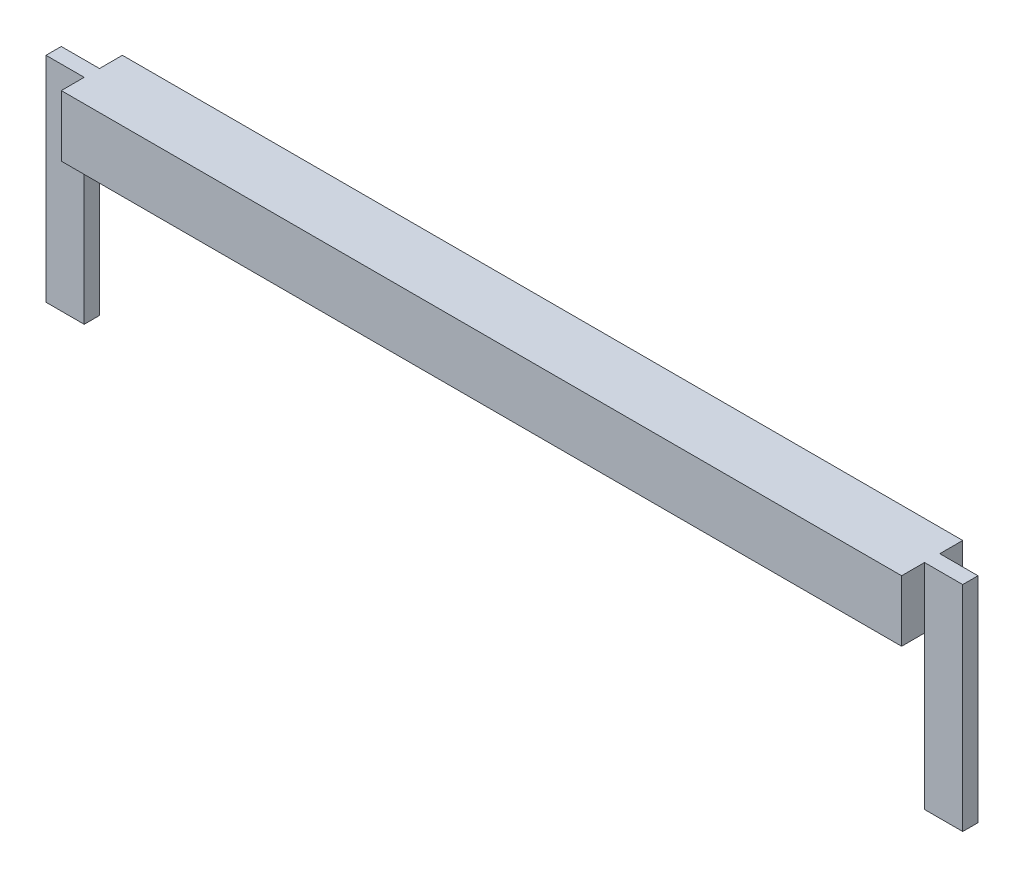
SolidWorks part; units mm, degrees
ref_plane "Front Plane" through (0, 0, 0) normal (0, 0, 1) x (1, 0, 0)
ref_plane "Top Plane" through (0, 0, 0) normal (0, 1, 0) x (1, 0, 0)
ref_plane "Right Plane" through (0, 0, 0) normal (1, 0, 0) x (0, 0, -1)
sketch "Sketch1" plane through (0, 0, 0) normal (0, 0, 1) x (1, 0, 0)
  line L1 (0, 0) -> (30, 0)
  line L2 (0, 0) -> (0, 2)
  line L3 (0, 2) -> (30, 2)
  line L4 (30, 0) -> (30, 2)
  dimension "D1" = 30
  dimension "D2" = 2
extrude "Boss-Extrude2" add sketch "Sketch1" along normal blind 0.5 contours L1 L4 L3 L2
sketch "Sketch2" plane through (0, 0, 0.5) normal (0, 0, 1) x (1, 0, 0)
  line L0 (1.25, 0) -> (1.25, 2)
  line L1 (0, 0) -> (30, 0) construction
  line L2 (0, 2) -> (30, 2) construction
  line L3 (1.25, 2) -> (28.75, 2)
  line L4 (28.75, 2) -> (28.75, 0)
  line L5 (28.75, 0) -> (1.25, 0)
  line L6 (0, 0) -> (0, 2) construction
  dimension "D1" = 27.5
  dimension "D2" = 1.25
extrude "Boss-Extrude4" add sketch "Sketch2" along normal blind 0.75 and the other way blind 1.25
sketch "Sketch3" plane through (0, 0, 0) normal (0, -1, 0) x (1, 0, 0)
  line L1 (0, 0) -> (1.25, 0)
  line L2 (0, 0) -> (0, 0.5)
  line L3 (0, 0.5) -> (1.25, 0.5)
  line L4 (1.25, 0) -> (1.25, 0.5)
extrude "Boss-Extrude5" add sketch "Sketch3" along normal blind 5
sketch "Sketch4" plane through (0, 0, 0) normal (0, -1, 0) x (-1, 0, 0)
  line L1 (-30, 0) -> (-28.75, 0)
  line L2 (-30, 0) -> (-30, -0.5)
  line L3 (-30, -0.5) -> (-28.75, -0.5)
  line L4 (-28.75, 0) -> (-28.75, -0.5)
extrude "Boss-Extrude6" add sketch "Sketch4" along normal blind 5
